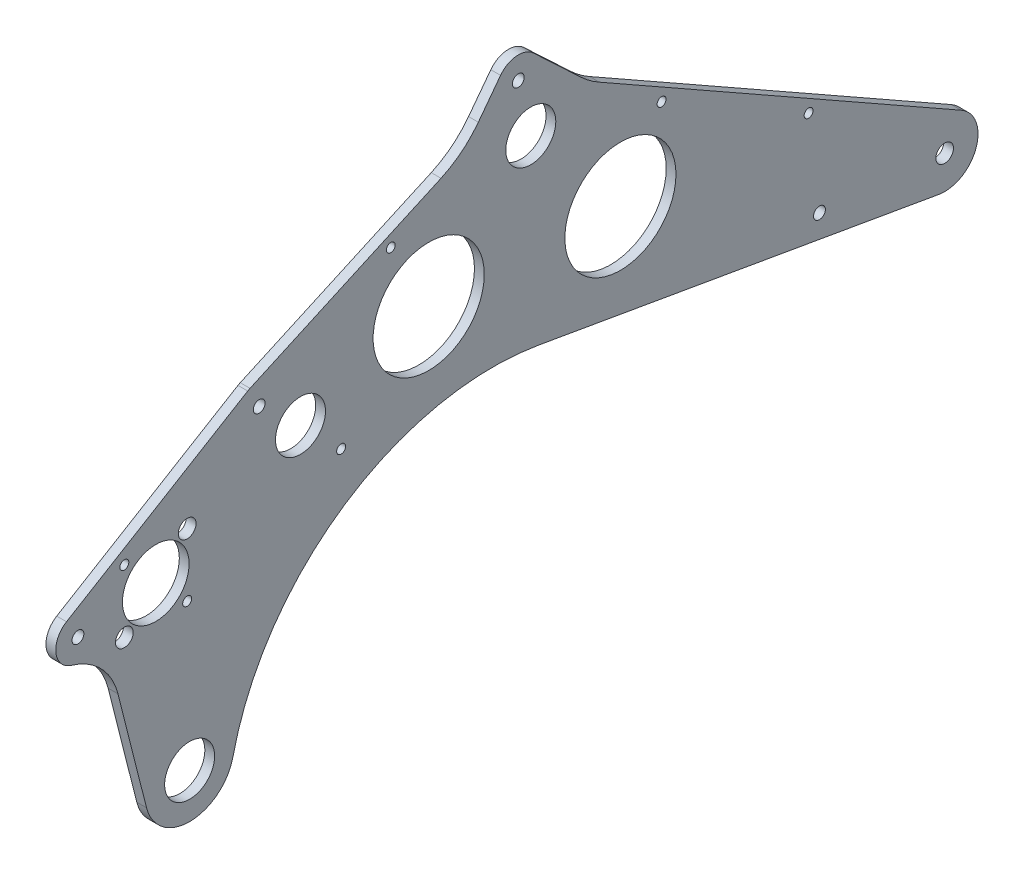
SolidWorks part; units mm, degrees
material "Acrylic (Medium-high impact)"
ref_plane "Front" through (0, 0, 0) normal (0, 0, 1) x (1, 0, 0)
ref_plane "Top" through (0, 0, 0) normal (0, 1, 0) x (1, 0, 0)
ref_plane "Right" through (0, 0, 0) normal (1, 0, 0) x (0, 0, -1)
sketch "Sketch1" plane through (0, 0, 0) normal (1, 0, 0) x (0, 0, -1)
  line L0 (-128.5875, -88.9) -> (-128.5875, -215.9)
  line L1 (-128.5875, -215.9) -> (-179.3875, -215.9)
  line L2 (-211.1375, -184.15) -> (-211.1375, -120.65)
  line L3 (-179.3875, -88.9) -> (-128.5875, -88.9)
  line L4 (-28.6872, -279.4) -> (-968.3377, -279.4) construction
  line L5 (-433.3875, -184.15) -> (-433.3875, -120.65) construction
  line L6 (-120.65, -76.2) -> (-95.25, -76.2)
  line L7 (-120.65, -76.2) -> (-120.65, -101.6)
  line L8 (-120.65, -101.6) -> (-95.25, -101.6)
  line L9 (-95.25, -76.2) -> (-95.25, -101.6)
  line L10 (-179.3875, 133.35) -> (-128.5875, 133.35) construction
  line L11 (-431.4942, -89.6952) -> (-179.3875, -120.65) construction
  line L12 (-368.1463, 49.3092) -> (-179.3875, -120.65) construction
  line L13 (-236.5251, 126.84) -> (-179.3875, -120.65) construction
  line L14 (-368.1463, 49.3092) -> (-344.9004, 26.0633) construction
  line L17 (-128.5875, -88.9) -> (-128.5875, 338.048) construction
  line L19 (-534.9875, 270.2474) -> (-534.9875, -123.3484) construction
  line L20 (-451.1462, -93.41) -> (-470.502, 8.9852)
  line L21 (-458.9454, 30.9884) -> (-376.2417, 67.5975)
  line L22 (-348.6741, 44.7449) -> (-352.6284, 27.8747)
  line L23 (-338.4951, 21.3754) -> (-252.6645, 138.6519)
  line L24 (-221.6622, 113.4574) -> (-416.6313, -103.0778)
  circle A0 centre (0, 0) radius 5.0419
  circle A1 centre (-431.4942, -89.6952) radius 11.557
  circle A2 centre (-368.1463, 49.3092) radius 11.557
  circle A3 centre (-236.5251, 126.84) radius 11.557
  arc A4 (-179.3875, -215.9) -> (-211.1375, -184.15) centre (-179.3875, -184.15) cw
  arc A5 (-211.1375, -120.65) -> (-179.3875, -88.9) centre (-179.3875, -120.65) cw
  circle A6 centre (-327.5258, -152.4) radius 120.65
  arc A7 (-433.3875, -120.65) -> (-179.3875, 133.35) centre (-179.3875, -120.65) cw construction
  circle A12 centre (-450.85, 12.7) radius 31.75
  arc A19 (-416.6313, -103.0778) -> (-451.1462, -93.41) centre (-431.4942, -89.6952) cw
  arc A20 (-470.502, 8.9852) -> (-458.9454, 30.9884) centre (-450.85, 12.7) cw
  arc A21 (-376.2417, 67.5975) -> (-348.6741, 44.7449) centre (-368.1463, 49.3092) cw
  arc A22 (-352.6284, 27.8747) -> (-338.4951, 21.3754) centre (-344.9004, 26.0633) ccw
  arc A23 (-252.6645, 138.6519) -> (-221.6622, 113.4574) centre (-236.5251, 126.84) cw
  circle B0 centre (-236.5251, 126.84) radius 20
  circle B1 centre (-368.1463, 49.3092) radius 20
  circle B2 centre (-431.4942, -89.6952) radius 20
  circle B3 centre (-450.85, 12.7) radius 20
  circle B4 centre (-344.9004, 26.0633) radius 7.9375
  dimension "D1" = 10.0838
  dimension "D2" = 23.114
  dimension "D4" = 31.75
  dimension "D10" = 241.3
  dimension "D19" = 63.5
  dimension "D22" = 322.2625
  dimension "D26" = 89.6952
  dimension "D27" = 431.4942
  dimension "D23" = 101.6
  dimension "D3" = 127
  dimension "D5" = 82.55
  dimension "D6" = 190.5
  dimension "D7" = 25.4
  dimension "D8" = 7.9375
  dimension "D9" = 203.2
  dimension "D12" = 120.65
  dimension "D13" = 76.2
  dimension "D14" = 35
  dimension "D15" = 35
  dimension "D16" = 7
  dimension "D24" = 406.4
  dimension "D25" = 45
  dimension "D11" = 222.25
sketch_block_instance "Block1-1"
sketch_block "Block1" parameters "D1"=40
sketch_block_instance "Block2-1"
sketch_block "Block2"
sketch_block_instance "Block3-1"
sketch_block "Block3"
sketch_block_instance "Block4-1"
sketch_block "Block4" parameters "D1"=40
sketch_block_instance "Block5-1"
sketch_block "Block5" parameters "D1"=15.875
other "Belt2"
sketch "Sketch3" plane through (0, 0, 0) normal (1, 0, 0) x (0, 0, -1)
  line L0 (-431.4942, -89.6952) -> (0, 0) construction
  line L1 (0, 0) -> (-71.5687, 6.2614) construction
  line L2 (0, 0) -> (-89.6952, 431.4942) construction
  line L3 (0, 0) -> (6.2614, 71.5687) construction
  line L4 (-71.5687, 6.2614) -> (-67.3566, -14.0015) construction
  line L5 (6.2614, 71.5687) -> (-14.0015, 67.3566) construction
  line L6 (6.2614, 71.5687) -> (-71.5687, 6.2614)
  line L7 (198.0154, 232.4693) -> (6.2614, 71.5687)
  line L8 (0, 0) -> (126.84, 236.5251) construction
  line L9 (0, 0) -> (-236.5251, 126.84) construction
  line L10 (-236.5251, 126.84) -> (-201.4538, -41.8764) construction
  line L11 (126.84, 236.5251) -> (-41.8764, 201.4538) construction
  circle A0 centre (-89.6952, 431.4942) radius 25.4
  dimension "D1" = 50.8
  dimension "D2" = 90
  dimension "D3" = 101.6
  dimension "D4" = 250.317
  dimension "D5" = 40
sketch "Sketch2" plane through (0, 0, 0) normal (1, 0, 0) x (0, 0, -1)
  line L0 (-456.1184, -95.9251) -> (-472.4688, -31.2987)
  line L1 (-501.8541, 19.0372) -> (-398.2953, 81.4322)
  line L2 (-431.4942, -89.6952) -> (-431.4942, 0) construction
  line L3 (-396.9762, 82.1249) -> (-287.8374, 131.5032)
  line L4 (9.3977, 16.5706) -> (-197.4399, 133.8741)
  line L6 (-232.0003, 21.0241) -> (-3.265, -18.7681)
  line L7 (-391.7411, 70.5541) -> (-368.1463, 49.3092) construction
  line L8 (-266.4972, 148.5827) -> (-253.8099, 165.4193)
  line L9 (-234.9643, 167.0255) -> (-208.0406, 141.6919)
  line L10 (-236.5251, 126.84) -> (-179.3875, -120.65) construction
  line L11 (-243.6673, 157.7762) -> (-236.5251, 126.84) construction
  line L12 (-236.5251, 126.84) -> (-201.4538, -41.8764) construction
  line L13 (-468.8105, -5.2605) -> (-432.8895, 30.6605) construction
  line L14 (-468.8105, 30.6605) -> (-432.8895, -5.2605) construction
  circle A0 centre (-236.5251, 126.84) radius 14.2875
  circle A1 centre (-368.1463, 49.3092) radius 14.2875
  circle A2 centre (-431.4942, -89.6952) radius 14.2875
  circle A3 centre (-450.85, 12.7) radius 19.05
  circle A4 centre (-344.9004, 26.0633) radius 2.5527
  circle A9 centre (0, 0) radius 5.0419 construction
  circle A10 centre (0, 0) radius 5.0419
  arc A13 (-456.1184, -95.9251) -> (-406.7265, -95.3274) centre (-431.4942, -89.6952) ccw
  arc A16 (-3.265, -18.7681) -> (9.3977, 16.5706) centre (0, 0) ccw
  arc A18 (-232.0003, 21.0241) -> (-406.7265, -95.3274) centre (-258.1205, -129.1208) ccw
  circle A19 centre (-71.5687, 6.2614) radius 3.3782
  circle A20 centre (-391.7411, 70.5541) radius 3.3782
  arc A21 (-398.2953, 81.4322) -> (-396.9762, 82.1249) centre (-391.7411, 70.5541) cw
  circle A22 centre (-243.6673, 157.7762) radius 3.3782
  arc A23 (-253.8099, 165.4193) -> (-234.9643, 167.0255) centre (-243.6673, 157.7762) cw
  circle A24 centre (-236.5251, 126.84) radius 25.4 construction
  arc A25 (-208.0406, 141.6919) -> (-197.4399, 133.8741) centre (-170.1967, 181.9112) ccw
  arc A26 (-266.4972, 148.5827) -> (-287.8374, 131.5032) centre (-310.6015, 181.8176) cw
  circle A27 centre (-432.8895, 30.6605) radius 5.08
  circle A28 centre (-468.8105, 30.6605) radius 2.5527
  circle A29 centre (-468.8105, -5.2605) radius 5.08
  circle A30 centre (-432.8895, -5.2605) radius 2.5527
  circle A31 centre (-450.85, 12.7) radius 25.4 construction
  circle A32 centre (-495.3, 8.1591) radius 3.3782
  arc A34 (-501.8541, 19.0372) -> (-498.8262, -4.0416) centre (-495.3, 8.1591) ccw
  arc A35 (-498.8262, -4.0416) -> (-472.4688, -31.2987) centre (-509.405, -40.6435) cw
  circle A37 centre (-450.85, 12.7) radius 31.75 construction
  dimension "D1" = 28.575
  dimension "D2" = 38.1
  dimension "D3" = 5.1054
  dimension "D4" = 50.8
  dimension "D5" = 12.7
  dimension "D6" = 6.7564
  dimension "D7" = 19.05
  dimension "D8" = 152.4
  dimension "D10" = 6.7564
  dimension "D11" = 12.7
  dimension "D12" = 31.75
  dimension "D13" = 12.7
  dimension "D14" = 31.75
  dimension "D17" = 55.2245
  dimension "D18" = 5.1054
  dimension "D19" = 10.16
  dimension "D20" = 50.8
  dimension "D21" = 25.4
  dimension "D22" = 38.1
  dimension "D23" = 44.45
  dimension "D9" = 25.4
  dimension "D15" = 50
  dimension "D16" = 35
extrude "Boss-Extrude1" add sketch "Sketch2" along normal blind 5.588
sketch "Sketch4" plane through (5.588, 0, 0) normal (1, 0, 0) x (0, 0, -1)
  line L0 (-368.1463, 49.3092) -> (-236.5251, 126.84) construction
  line L1 (-316.1822, 118.679) -> (-294.8849, 71.6064) construction
  line L2 (-287.8374, 131.5032) -> (-396.9762, 82.1249) construction
  line L3 (-294.8849, 71.6064) -> (-285.5767, 20.7856) construction
  line L4 (-285.5767, 20.7856) -> (-258.1205, -129.1208) construction
  line L5 (-159.3107, 112.25) -> (-185.3125, 66.4018) construction
  line L6 (9.3977, 16.5706) -> (-197.4399, 133.8741) construction
  line L7 (-185.3125, 66.4018) -> (-194.3463, 14.4736) construction
  line L8 (-232.0003, 21.0241) -> (-3.265, -18.7681) construction
  line L9 (-391.7411, 70.5541) -> (-243.6673, 157.7762) construction
  line L10 (-319.1408, 117.3404) -> (-317.7042, 114.1652) construction
  line L11 (-245.8065, 154.0041) -> (-161.7827, 106.3518) construction
  line L12 (-161.7827, 106.3518) -> (-77.7588, 58.6994) construction
  line L13 (-77.7588, 58.6994) -> (6.2651, 11.0471) construction
  line L14 (-245.8065, 154.0041) -> (-243.6673, 157.7762) construction
  line L15 (0, 0) -> (6.2651, 11.0471) construction
  circle A0 centre (-294.8849, 71.6064) radius 31.75
  circle A1 centre (-185.3125, 66.4018) radius 31.75
  arc A2 (-232.0003, 21.0241) -> (-406.7265, -95.3274) centre (-258.1205, -129.1208) ccw construction
  circle A3 centre (-316.5233, 111.555) radius 2.54
  circle A5 centre (-161.7827, 106.3518) radius 2.54
  circle A6 centre (-77.7588, 58.6994) radius 2.54
  point P2 (-302.3357, 88.0746)
  dimension "D1" = 63.5
  dimension "D2" = 63.5
  dimension "D3" = 196.85
  dimension "D4" = 5.08
  dimension "D5" = 6.35
  dimension "D6" = 6.35
extrude "Cut-Extrude1" cut sketch "Sketch4" against normal through all
